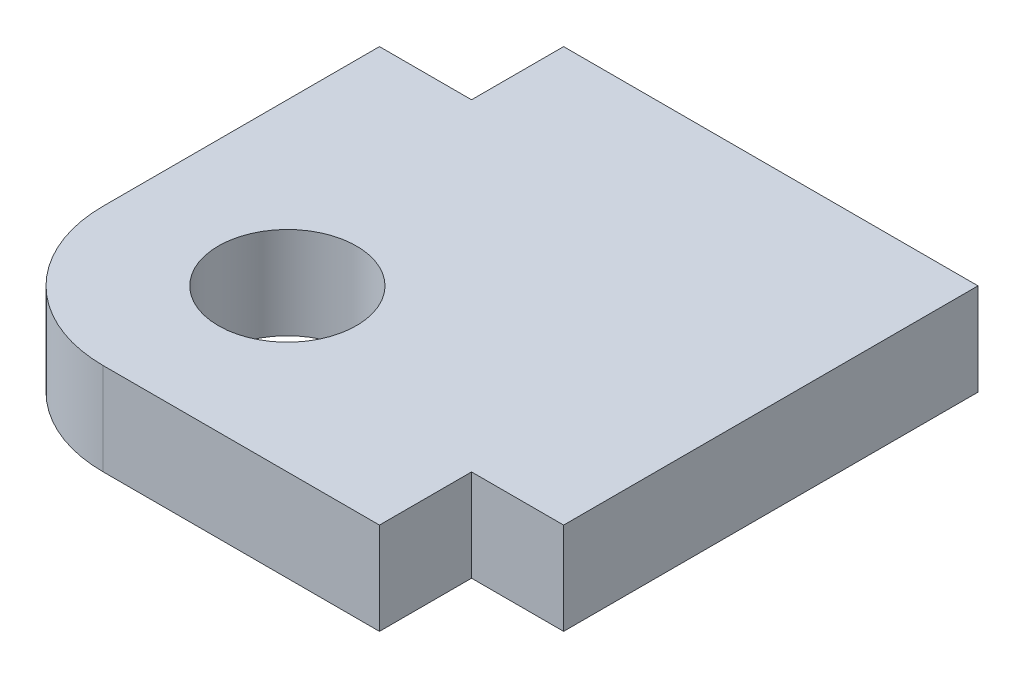
SolidWorks part; units mm, degrees
ref_plane "Front Plane" through (0, 0, 0) normal (0, 0, 1) x (1, 0, 0)
ref_plane "Top Plane" through (0, 0, 0) normal (0, 1, 0) x (1, 0, 0)
ref_plane "Right Plane" through (0, 0, 0) normal (1, 0, 0) x (0, 0, -1)
sketch "Sketch1" plane through (0, 0, 0) normal (0, 1, 0) x (1, 0, 0)
  line L0 (6.3777, 5.9389) -> (-2.6223, 5.9389)
  line L1 (-2.6223, 5.9389) -> (-2.6223, 3.9389)
  line L2 (-2.6223, 3.9389) -> (-4.6223, 3.9389)
  line L3 (-4.6223, 3.9389) -> (-4.6223, -2.0611)
  line L4 (-1.6223, -5.0611) -> (4.3777, -5.0611)
  line L5 (4.3777, -5.0611) -> (4.3777, -3.0611)
  line L6 (4.3777, -3.0611) -> (6.3777, -3.0611)
  line L7 (6.3777, -3.0611) -> (6.3777, 5.9389)
  arc A0 (-4.6223, -2.0611) -> (-1.6223, -5.0611) centre (-1.6223, -2.0611) ccw
  circle A1 centre (-1.1223, -1.5611) radius 1.5
extrude "Boss-Extrude1" add sketch "Sketch1" along normal blind 2
